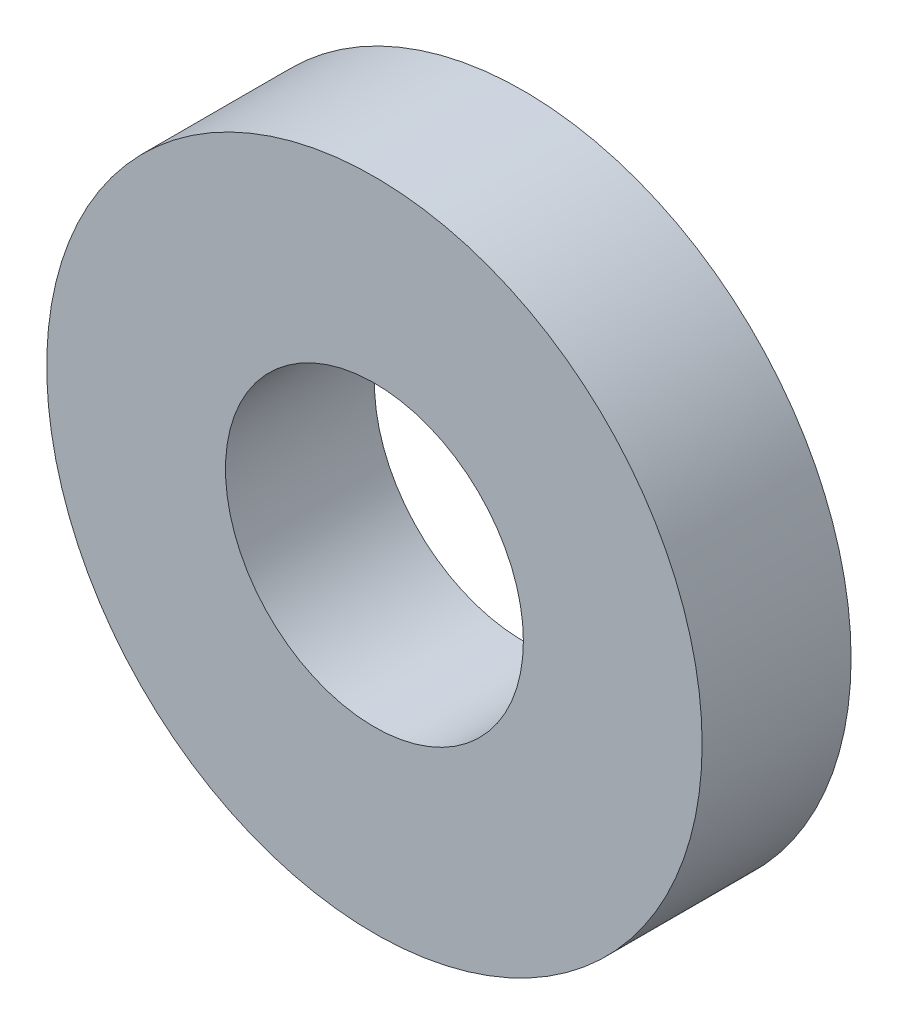
SolidWorks part; units mm, degrees
ref_plane "Front Plane" through (0, 0, 0) normal (0, 0, 1) x (1, 0, 0)
ref_plane "Top Plane" through (0, 0, 0) normal (0, 1, 0) x (1, 0, 0)
ref_plane "Right Plane" through (0, 0, 0) normal (1, 0, 0) x (0, 0, -1)
sketch "Sketch1" plane through (0, 0, 0) normal (0, 0, 1) x (1, 0, 0)
  circle A0 centre (0, 0) radius 6
  circle A1 centre (0, 0) radius 13.2
extrude "Boss-Extrude1" add sketch "Sketch1" along normal blind 6
sketch "Sketch2" plane through (0, 0, 6) normal (0, 0, 1) x (1, 0, 0)
  line L0 (0, 0) -> (0, 15.2) construction
  line L1 (-1.8199, 15.2) -> (0, 0) construction
  line L2 (1.8199, 15.2) -> (0, 0) construction
  arc A0 (-1.8199, 12) -> (1.8199, 12) centre (0, 0) cw
  arc A1 (-2.8199, 12.8953) -> (2.8199, 12.8953) centre (0, 0) cw
  arc A2 (-1.8199, 10.512) -> (1.8199, 10.512) centre (0, 0) cw
  arc A3 (-2.8199, 12.8953) -> (-1.8199, 10.512) centre (-3.5115, 11.2036) cw
  arc A4 (2.8199, 12.8953) -> (1.8199, 10.512) centre (3.5115, 11.2036) ccw
